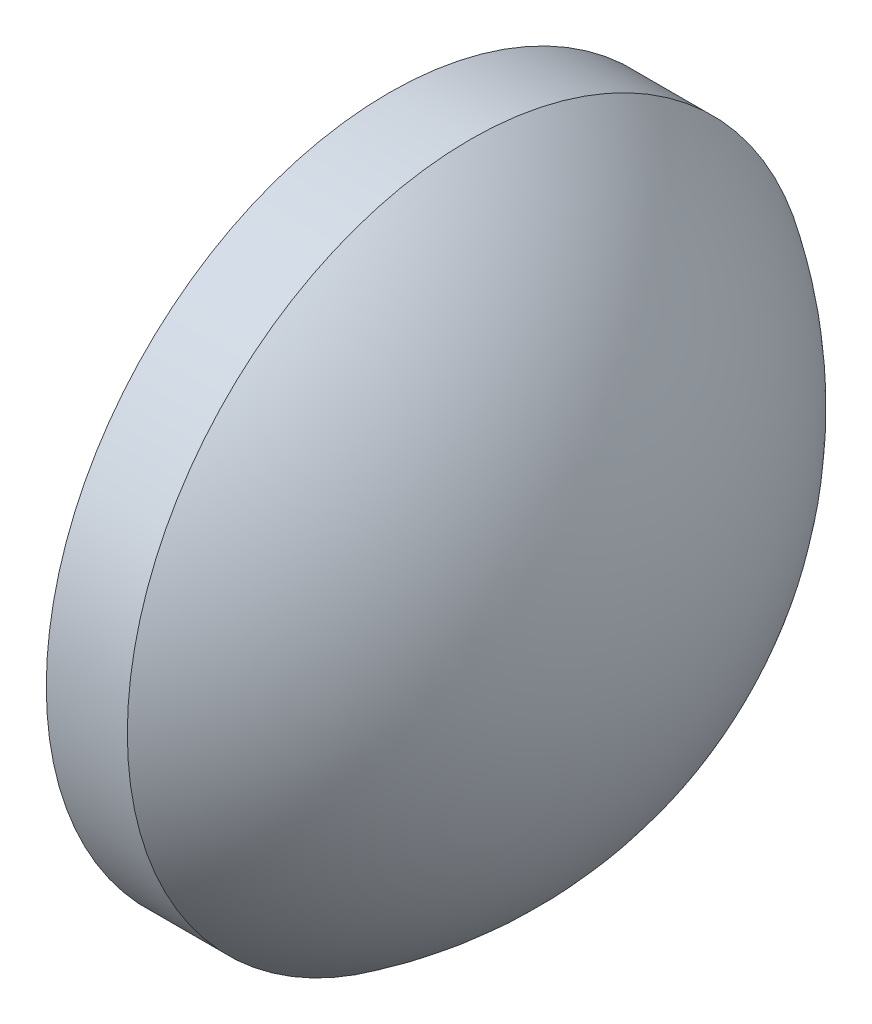
SolidWorks part; units mm, degrees
ref_plane "前视基准面" through (0, 0, 0) normal (0, 0, 1) x (1, 0, 0)
ref_plane "上视基准面" through (0, 0, 0) normal (0, 1, 0) x (1, 0, 0)
ref_plane "右视基准面" through (0, 0, 0) normal (1, 0, 0) x (0, 0, -1)
sketch "草图1" plane through (0, 0, 0) normal (0, 0, 1) x (1, 0, 0)
  line L0 (110.1654, 65.2336) -> (128.9614, 65.2336) construction
  line L1 (115.7736, 65.2336) -> (115.7736, 77.9336)
  line L2 (115.7736, 77.9336) -> (118.7755, 77.9336)
  line L3 (125.6836, 65.2336) -> (115.7736, 65.2336)
  arc A0 (125.6836, 65.2336) -> (118.7755, 77.9336) centre (110.5556, 65.2336) ccw
  dimension "D1" = 15.128
revolve "旋转1" add sketch "草图1" angle 360 about L0
